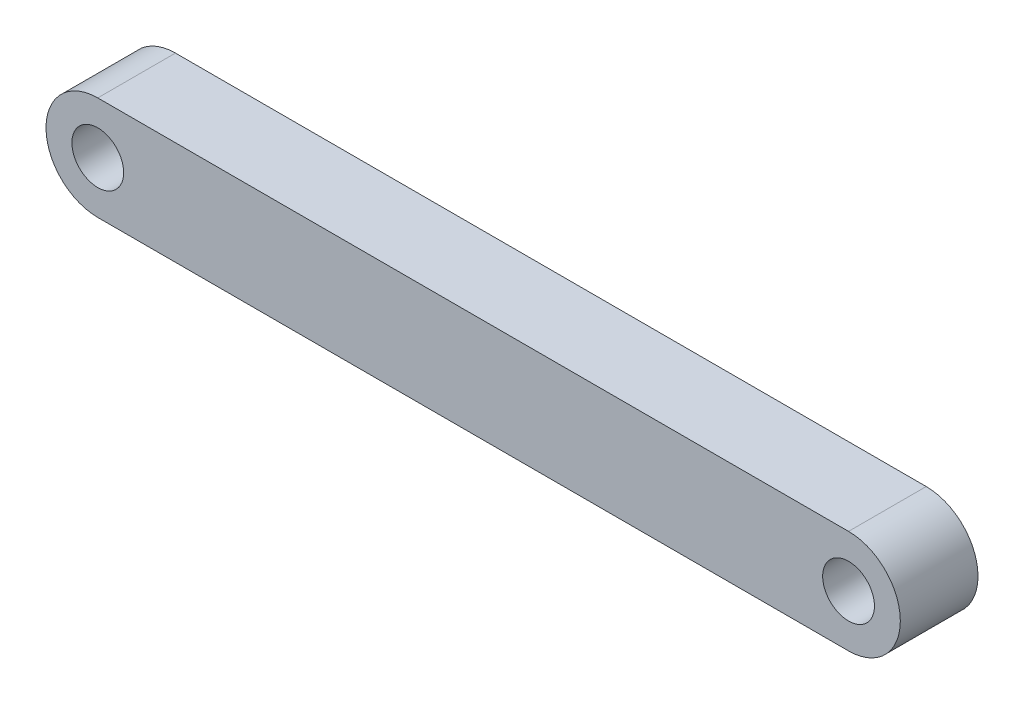
SolidWorks part; units mm, degrees
ref_plane "Спереди" through (0, 0, 0) normal (0, 0, 1) x (1, 0, 0)
ref_plane "Сверху" through (0, 0, 0) normal (0, 1, 0) x (1, 0, 0)
ref_plane "Справа" through (0, 0, 0) normal (1, 0, 0) x (0, 0, -1)
sketch "Эскиз1" plane through (0, 0, 0) normal (0, 0, 1) x (1, 0, 0)
  line L0 (-17.3575, -5.4234) -> (36.8251, 20.3496) construction
  line L1 (-2715.2651, -523.2425) -> (-2635.2651, -523.2425) construction
  line L2 (-40.1408, -46.1699) -> (39.8592, -46.1699) construction
  line L6 (0, 0) -> (-290, 0) construction
  line L7 (0, 20) -> (-290, 20)
  line L8 (0, -20) -> (-290, -20)
  line L12 (0, 0) -> (-50000, 0) construction
  line L13 (0, 0) -> (37157.2413, 33456.5303) construction
  circle A6 centre (-290, 0) radius 10
  circle A7 centre (0, 0) radius 10
  arc A8 (-290, -20) -> (-290, 20) centre (-290, 0) cw
  arc A10 (0, 20) -> (0, -20) centre (0, 0) cw
  dimension "D4" = 20
  dimension "D5" = 20
  dimension "D6" = 42
  dimension "D3" = 20
  dimension "D1" = 290
  dimension "D2" = 80
extrude "Бобышка-Вытянуть1" add sketch "Эскиз1" along normal mid plane 30
